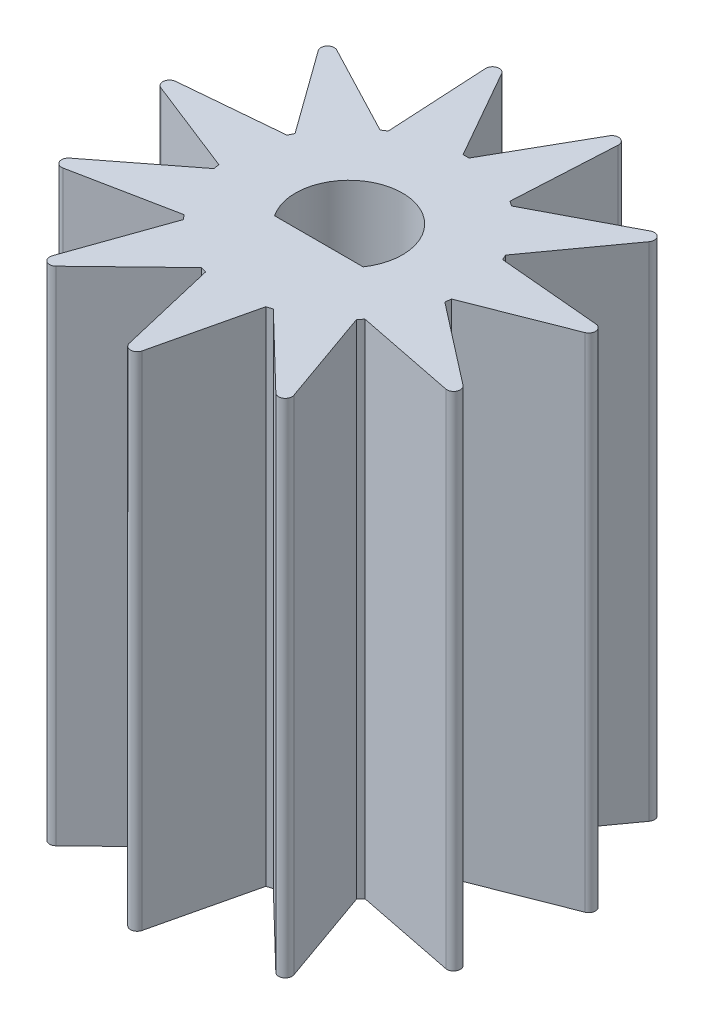
SolidWorks part; units mm, degrees
material "ABS"
ref_plane "Plano frontal" through (0, 0, 0) normal (0, 0, 1) x (1, 0, 0)
ref_plane "Plano superior" through (0, 0, 0) normal (0, 1, 0) x (1, 0, 0)
ref_plane "Plano direito" through (0, 0, 0) normal (1, 0, 0) x (0, 0, -1)
sketch "Esboço1" plane through (0, 0, 0) normal (0, 0, 1) x (1, 0, 0)
  line L0 (0, 0) -> (0, 9.0846) construction
  line L1 (3.5, 15) -> (1.6, 15)
  line L2 (1.6, 15) -> (1.6, 0)
  line L3 (3.5, 15) -> (3.5, 0)
  line L4 (3.5, 0) -> (1.6, 0)
  dimension "D1" = 7
  dimension "D2" = 3.2
  dimension "D5" = 15
revolve "Revolução1" add sketch "Esboço1" angle 360 about L0
sketch "Esboço3" plane through (0, 0, 0) normal (0, -1, 0) x (-1, 0, 0)
  line L0 (0, -3.5) -> (0, -7.2) construction
  line L1 (-0.1947, -6.3743) -> (-0.9, -3.3823)
  line L2 (0.1947, -6.3743) -> (0.9, -3.3823)
  circle A0 centre (0, 0) radius 3.5 construction
  arc A1 (0.9, -3.3823) -> (-0.9, -3.3823) centre (0, 0) cw
  arc A2 (-0.1947, -6.3743) -> (0.1947, -6.3743) centre (0, -6.3284) ccw
  dimension "D3" = 0.2
  dimension "D1" = 7.2
  dimension "D2" = 1.8
extrude "Ressalto-extrusão1" add sketch "Esboço3" against normal up to surface (15 mm away) up to face at (0, 15, -1.6)
pattern_circular "PadrãoCircular1" count 11 over 360 about axis through (0, 0, 0) along (0, 1, 0) of "Ressalto-extrusão1"
sketch "Esboço4" plane through (0, 0, 0) normal (0, -1, 0) x (1, 0, 0)
  line L0 (1.3229, 0.9) -> (-1.3229, 0.9)
  arc A0 (1.3229, 0.9) -> (-1.3229, 0.9) centre (0, 0) ccw
  circle A1 centre (0, 0) radius 1.6 construction
  dimension "D1" = 2.5
extrude "Ressalto-extrusão2" add sketch "Esboço4" against normal up to surface (15 mm away)
